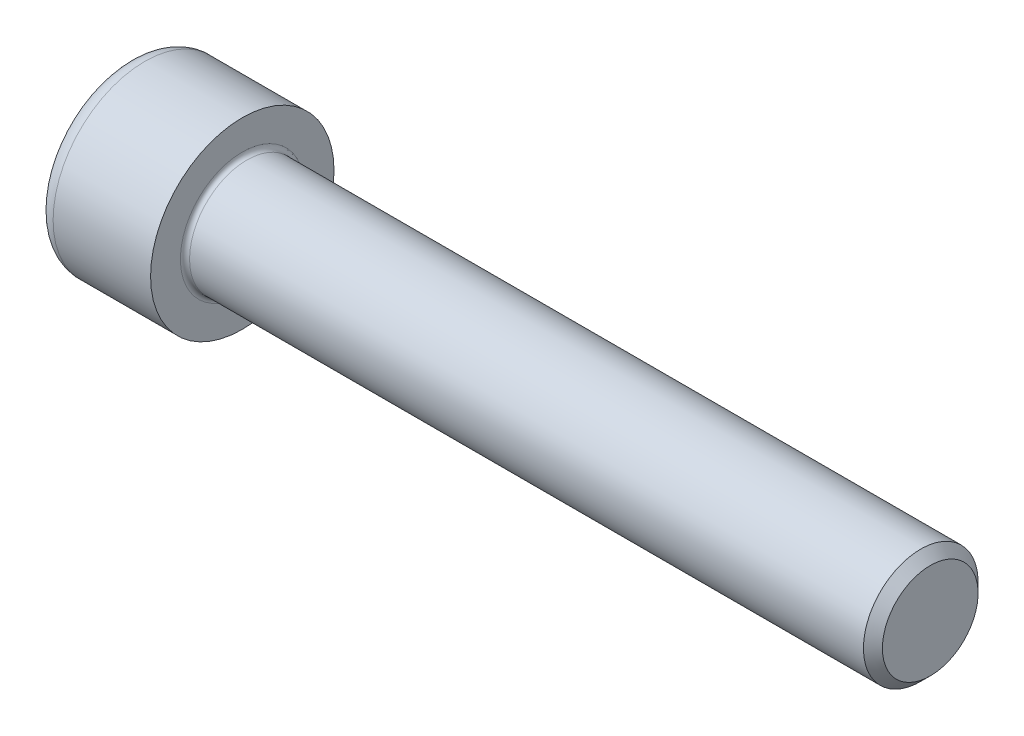
SolidWorks part; units mm, degrees
revolve "Base-Revolve" add sketch "BodySke"
sketch "BodySke" plane through (0, 0, 0) normal (0, 0, 1) x (1, 0, 0)
  line L0 (0, 0) -> (0, 8)
  line L1 (0, 8) -> (10, 8)
  line L2 (10, 8) -> (10, 5)
  line L3 (10, 5) -> (69.172, 5)
  line L4 (70, 4.172) -> (70, 0)
  line L5 (70, 0) -> (0, 0)
  line L6 (-31.75, 0) -> (127, 0) construction
  line L8 (70, 4.172) -> (69.172, 5)
  line L10 (70, -4.172) -> (69.172, -5) construction
  line L11 (11.5, 9.525) -> (11.5, 3.175) construction
  line L12 (38, 9.525) -> (38, 3.175) construction
  line L13 (10, 9.525) -> (10, 3.175) construction
  dimension "Body_ch_ang" = 45
  dimension "Thread_length" = 60
cosmetic thread "ThreadCosmetic" [suppressed]
fillet "Fillet1" radius 0.4 1 edges at (10, 0, 5)
fillet "Fillet2" radius 1.5 1 edges at (0, 0, 8)
ref_plane "Plane1" through (0, 0, 0) normal (0, 0, 1) x (1, 0, 0)
ref_plane "Plane2" through (0, 0, 0) normal (0, 1, 0) x (1, 0, 0)
ref_plane "Plane3" through (0, 0, 0) normal (1, 0, 0) x (0, 0, -1)
other "Configuration Table"
sketch "Sketch2" plane through (0, 0, 0) normal (0, 0, 1) x (1, 0, 0)
  line L0 (0, 4.0575) -> (5, 4.0575)
  line L1 (5, 4.0575) -> (7.3426, 0)
  line L2 (-31.75, 0) -> (127, 0) construction
  line L3 (7.3426, 0) -> (0, 0)
  line L4 (0, 0) -> (0, 4.0575)
  line L6 (0, 0) -> (47.625, 0) construction
  dimension "D2" = 60
revolve "Hex-PreBroach" cut sketch "Sketch2" angle 360 about L6
sketch "Sketch3" plane through (0, 0, 0) normal (-1, 0, 0) x (0, 0.5, 0.866)
  line L0 (2.3426, 4.0575) -> (-2.3426, 4.0575)
  line L1 (-2.3426, 4.0575) -> (-4.6852, 0)
  line L2 (2.3426, 4.0575) -> (4.6852, 0)
  line L3 (2.3426, -4.0575) -> (4.6852, 0)
  line L4 (2.3426, -4.0575) -> (-2.3426, -4.0575)
  line L5 (-2.3426, -4.0575) -> (-4.6852, 0)
extrude "Hex" cut sketch "Sketch3" against normal blind 5
sketch "ThdSchSke" plane through (0, 0, 0) normal (0, 0, 1) x (1, 0, 0)
  line L0 (38, -4.172) -> (37.4202, -5)
  line L1 (38, -4.172) -> (38.5798, -5)
  line L2 (38.5798, -5) -> (38.5798, -6.25)
  line L3 (-3.175, 0) -> (5.1513, 0) construction
  line L4 (0, 6.5) -> (0, -6.5) construction
  line L5 (38.5798, -6.25) -> (37.4202, -6.25)
  line L6 (37.4202, -6.25) -> (37.4202, -5)
revolve "ThreadSchematic" [suppressed] cut sketch "ThdSchSke" angle 360 about L3
pattern_linear "ThdSchPat" [suppressed]
equation "\"D2@Sketch3\" = \"Hex_size@Sketch3\" / 2"
equation "\"D1@Sketch3\" = \"Hex_size@Sketch3\" / 2"
equation "\"D1@Sketch2\" = \"Hex_size@Sketch3\" / 2"
equation "\"Thread_minor@ThreadCosmetic\"  =  \"Minor_dia@BodySke\""
equation "\"Depth@Sketch2\" =  \"Key_eng@Hex\""
equation "\"Thread_length@ThreadCosmetic\" = ((sgn( (\"Length@BodySke\" - \"Advance@BodySke\" * 3.0) - \"Thread_nom@BodySke\" )-1)*( (\"Length@BodySke\" - \"Advance@BodySke\" * 3.0) - \"Thread_nom@BodySke\" ))/-2+ \"Thread_nom@BodySke\""
equation "\"Thread_minor@ThdSchSke\" = \"Minor_dia@BodySke\""
equation "\"Diameter@ThdSchSke\" = \"Diameter@BodySke\""
equation "\"Overcut@ThdSchSke\" = \"Diameter@BodySke\" * 1.25"
equation "\"Start@ThdSchSke\" = \"Head_ht@BodySke\" + \"Length@BodySke\" - \"Thread_length@ThreadCosmetic\"  '---Non-countersunk---"
equation "\"Num_threads@ThdSchPat\" = int( \"Thread_length@ThreadCosmetic\" / \"Advance@BodySke\" + 0.999 )  + 1"
equation "\"Advance@ThdSchPat\" = \"Thread_length@ThreadCosmetic\" /  (\"Num_threads@ThdSchPat\" - 1) 'relax it"
equation "\"Num_threads@ThdSchPat\" = \"Num_threads@ThdSchPat\" - sgn( \"Num_threads@ThdSchPat\" - 1) '---chamfered tips only---"
